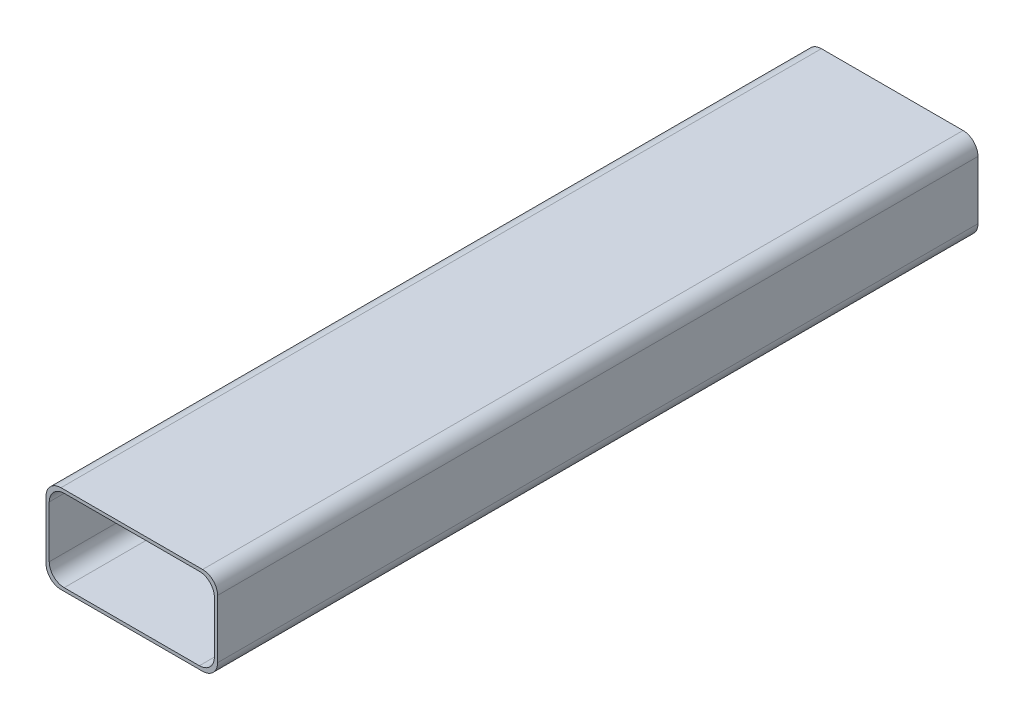
SolidWorks part; units mm, degrees
material "Zoltek Panex 33"
ref_plane "Front Plane" through (0, 0, 0) normal (0, 0, 1) x (1, 0, 0)
ref_plane "Top Plane" through (0, 0, 0) normal (0, 1, 0) x (1, 0, 0)
ref_plane "Right Plane" through (0, 0, 0) normal (1, 0, 0) x (0, 0, -1)
sketch "Sketch1" plane through (0, 0, 0) normal (0, 0, 1) x (1, 0, 0)
  line L1 (-45.1561, -27.305) -> (45.1561, -27.305)
  line L2 (-55.1561, -17.305) -> (-55.1561, 17.305)
  line L3 (-45.1561, 27.305) -> (45.1561, 27.305)
  line L4 (55.1561, -17.305) -> (55.1561, 17.305)
  line L5 (-55.1561, -27.305) -> (55.1561, 27.305) construction
  line L6 (-55.1561, 27.305) -> (55.1561, -27.305) construction
  line L7 (-47.3151, -29.464) -> (47.3151, -29.464)
  line L8 (-57.3151, -19.464) -> (-57.3151, 19.464)
  line L9 (-47.3151, 29.464) -> (47.3151, 29.464)
  line L10 (57.3151, -19.464) -> (57.3151, 19.464)
  line L11 (-57.3151, -29.464) -> (57.3151, 29.464) construction
  line L12 (-57.3151, 29.464) -> (57.3151, -29.464) construction
  arc A0 (45.1561, -27.305) -> (55.1561, -17.305) centre (45.1561, -17.305) ccw
  arc A1 (-45.1561, -27.305) -> (-55.1561, -17.305) centre (-45.1561, -17.305) cw
  arc A2 (-55.1561, 17.305) -> (-45.1561, 27.305) centre (-45.1561, 17.305) cw
  arc A3 (45.1561, 27.305) -> (55.1561, 17.305) centre (45.1561, 17.305) cw
  arc A4 (47.3151, -29.464) -> (57.3151, -19.464) centre (47.3151, -19.464) ccw
  arc A5 (-47.3151, -29.464) -> (-57.3151, -19.464) centre (-47.3151, -19.464) cw
  arc A6 (-57.3151, 19.464) -> (-47.3151, 29.464) centre (-47.3151, 19.464) cw
  arc A7 (47.3151, 29.464) -> (57.3151, 19.464) centre (47.3151, 19.464) cw
  point P0 (0, 0)
  point P18 (0, 0)
  dimension "D3" = 10
  dimension "D6" = 10
  dimension "D1" = 110.3122
  dimension "D2" = 54.61
  dimension "D4" = 2.159
  dimension "D5" = 2.159
extrude "Boss-Extrude1" add sketch "Sketch1" along normal blind 508
